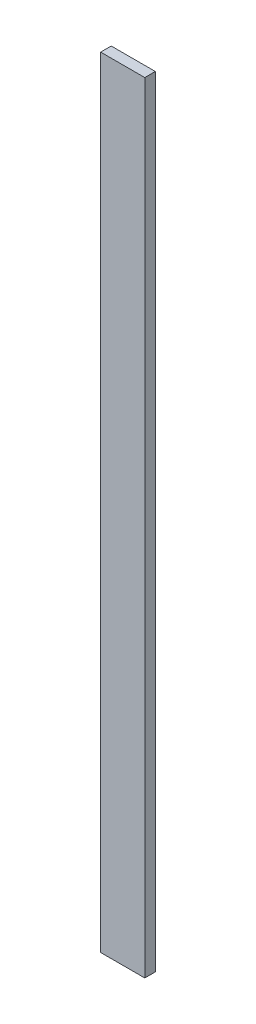
SolidWorks part; units mm, degrees
material "Plain Carbon Steel"
ref_plane "Front Plane" through (0, 0, 0) normal (0, 0, 1) x (1, 0, 0)
ref_plane "Top Plane" through (0, 0, 0) normal (0, 1, 0) x (1, 0, 0)
ref_plane "Right Plane" through (0, 0, 0) normal (1, 0, 0) x (0, 0, -1)
sketch "Sketch1" plane through (0, 0, 0) normal (0, 1, 0) x (1, 0, 0)
  line L1 (0, 0) -> (6.35, 0)
  line L2 (0, 0) -> (0, 1.5189)
  line L3 (0, 1.5189) -> (6.35, 1.5189)
  line L4 (6.35, 0) -> (6.35, 1.5189)
  dimension "D1" = 6.35
  dimension "D2" = 1.5189
extrude "Boss-Extrude1" add sketch "Sketch1" along normal blind 112.268
